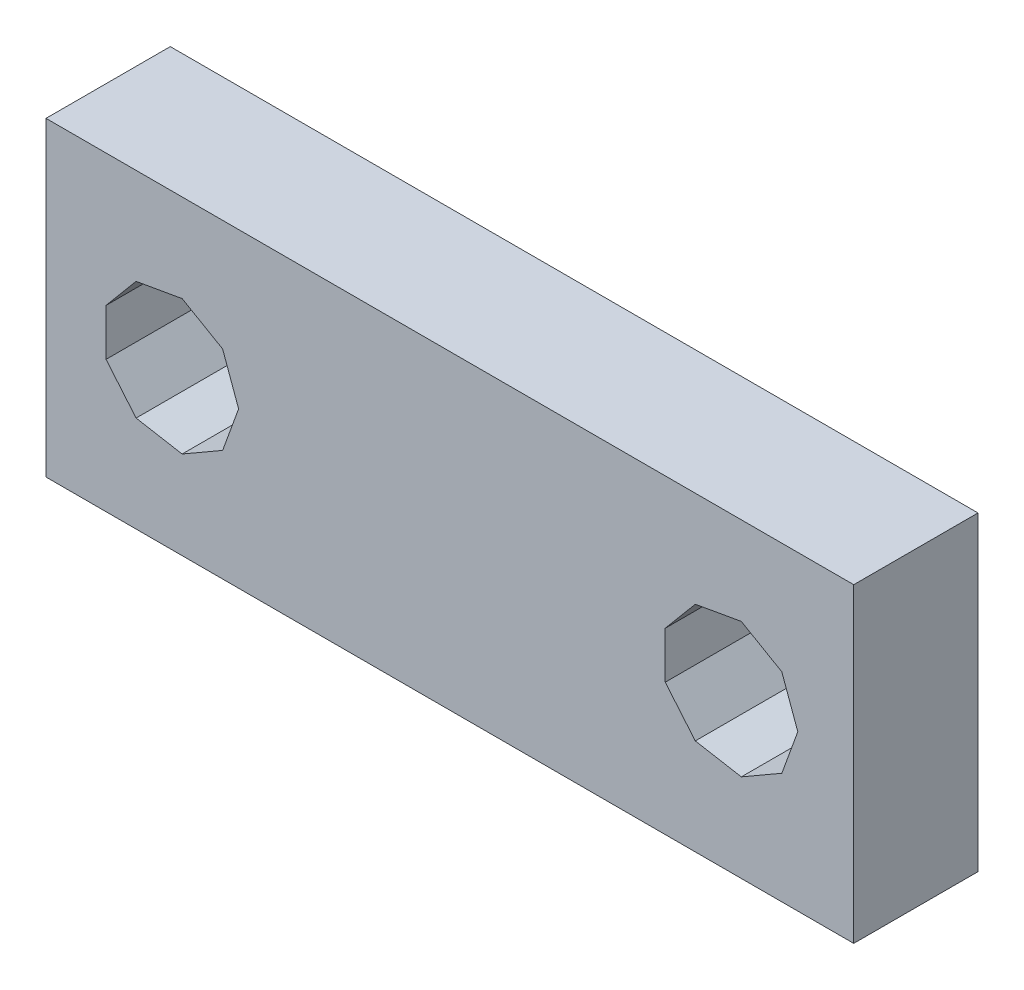
SolidWorks part; units mm, degrees
ref_plane "Front Plane" through (0, 0, 0) normal (0, 0, 1) x (1, 0, 0)
ref_plane "Top Plane" through (0, 0, 0) normal (0, 1, 0) x (1, 0, 0)
ref_plane "Right Plane" through (0, 0, 0) normal (1, 0, 0) x (0, 0, -1)
sketch "Sketch1" plane through (0, 0, 0) normal (0, 0, 1) x (1, 0, 0)
  line L0 (2.9, 6.9053) -> (4.382, 7.1666)
  line L1 (0, 10) -> (26, 10)
  line L2 (0, 10) -> (0, 0)
  line L3 (0, 0) -> (26, 0)
  line L4 (26, 10) -> (26, 0)
  line L5 (4.382, 7.1666) -> (5.6853, 6.4141)
  line L6 (5.6853, 6.4141) -> (6.2, 5)
  line L7 (6.2, 5) -> (5.6853, 3.5859)
  line L8 (5.6853, 3.5859) -> (4.382, 2.8334)
  line L9 (4.382, 2.8334) -> (2.9, 3.0947)
  line L10 (2.9, 3.0947) -> (1.9327, 4.2476)
  line L11 (1.9327, 4.2476) -> (1.9327, 5.7524)
  line L12 (1.9327, 5.7524) -> (2.9, 6.9053)
  line L13 (20.9, 6.9053) -> (22.382, 7.1666)
  line L14 (22.382, 7.1666) -> (23.6853, 6.4141)
  line L15 (23.6853, 6.4141) -> (24.2, 5)
  line L16 (24.2, 5) -> (23.6853, 3.5859)
  line L17 (23.6853, 3.5859) -> (22.382, 2.8334)
  line L18 (22.382, 2.8334) -> (20.9, 3.0947)
  line L19 (20.9, 3.0947) -> (19.9327, 4.2476)
  line L20 (19.9327, 4.2476) -> (19.9327, 5.7524)
  line L23 (19.9327, 5.7524) -> (20.9, 6.9053)
  dimension "D1" = 26
  dimension "D2" = 10
  dimension "D3" = 1.9327
  dimension "D4" = 2.9
  dimension "D5" = 4.382
  dimension "D6" = 5.6853
  dimension "D7" = 6.2
  dimension "D8" = 19.9327
  dimension "D9" = 2.8334
extrude "Boss-Extrude1" add sketch "Sketch1" along normal blind 4
